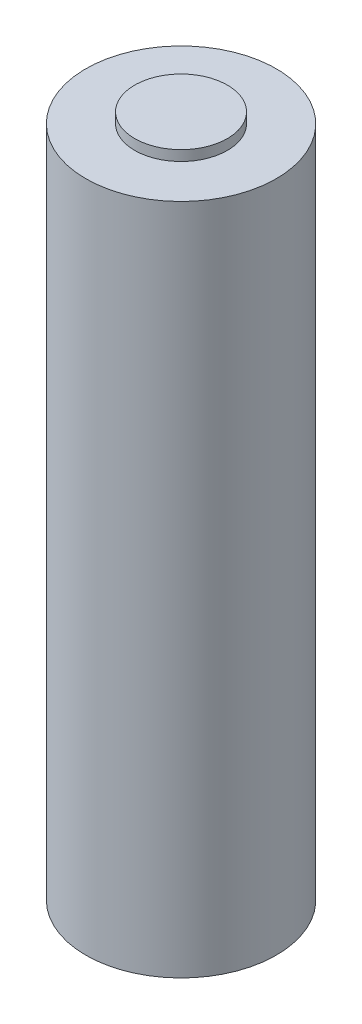
SolidWorks part; units mm, degrees
ref_plane "Front Plane" through (0, 0, 0) normal (0, 0, 1) x (1, 0, 0)
ref_plane "Top Plane" through (0, 0, 0) normal (0, 1, 0) x (1, 0, 0)
ref_plane "Right Plane" through (0, 0, 0) normal (1, 0, 0) x (0, 0, -1)
sketch "Sketch1" plane through (0, 0, 0) normal (0, 1, 0) x (1, 0, 0)
  circle A0 centre (0, 0) radius 9.25
  dimension "D1" = 18.5
extrude "Boss-Extrude1" add sketch "Sketch1" along normal blind 65.3 contours A0
sketch "Sketch2" plane through (0, 65.3, 0) normal (0, 1, 0) x (1, 0, 0)
  circle A0 centre (0, 0) radius 4.5
  dimension "D1" = 9
extrude "Boss-Extrude2" add sketch "Sketch2" along normal blind 1
